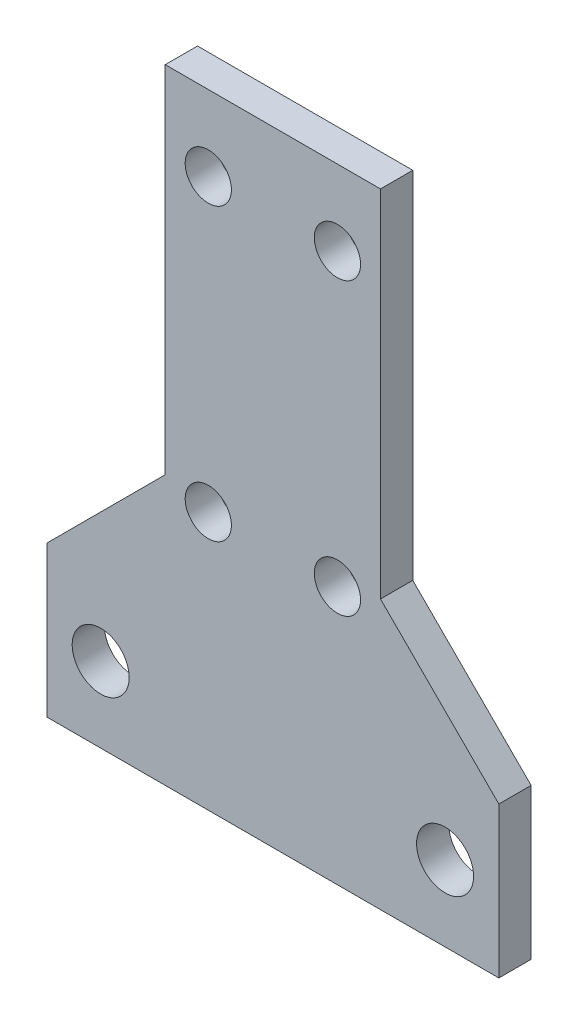
SolidWorks part; units mm, degrees
material "Thornel Mat VMA"
ref_plane "前视基准面" through (0, 0, 0) normal (0, 0, 1) x (1, 0, 0)
ref_plane "上视基准面" through (0, 0, 0) normal (0, 1, 0) x (1, 0, 0)
ref_plane "右视基准面" through (0, 0, 0) normal (1, 0, 0) x (0, 0, -1)
sketch "Sketch2" plane through (0, 0, 0) normal (0, 0, 1) x (1, 0, 0)
  line L0 (-392.4899, 179) -> (-392.4899, 165) construction
  line L1 (-434.4899, 165) -> (-392.4899, 165)
  line L2 (-434.4899, 165) -> (-434.4899, 179)
  line L3 (-423.4899, 223) -> (-403.4899, 223)
  line L4 (-392.4899, 165) -> (-392.4899, 179)
  line L5 (-413.4899, 223) -> (-413.4899, 165) construction
  line L6 (-407.4899, 216) -> (-407.4899, 189) construction
  line L7 (-403.4899, 260) -> (-403.4899, 20) construction
  line L8 (-392.4899, 179) -> (-403.4899, 190)
  line L9 (-403.4899, 190) -> (-403.4899, 223)
  line L10 (-434.4899, 179) -> (-392.4899, 179) construction
  line L11 (-423.4899, 190) -> (-423.4899, 223)
  line L12 (-434.4899, 179) -> (-423.4899, 190)
  circle A1 centre (-397.4899, 172) radius 2.65
  circle A2 centre (-407.4899, 216) radius 2.15
  circle A3 centre (-407.4899, 189) radius 2.15
  circle A4 centre (-429.4899, 172) radius 2.65
  circle A5 centre (-419.4899, 189) radius 2.15
  circle A6 centre (-419.4899, 216) radius 2.15
  dimension "D1" = 4.3
  dimension "D2" = 7
  dimension "D3" = 5
  dimension "D4" = 5.3
  dimension "D6" = 17
  dimension "D8" = 7
  dimension "D5" = 27
  dimension "D7" = 4
  dimension "D9" = 45
extrude "Boss-Extrude1" add sketch "Sketch2" along normal blind 3
